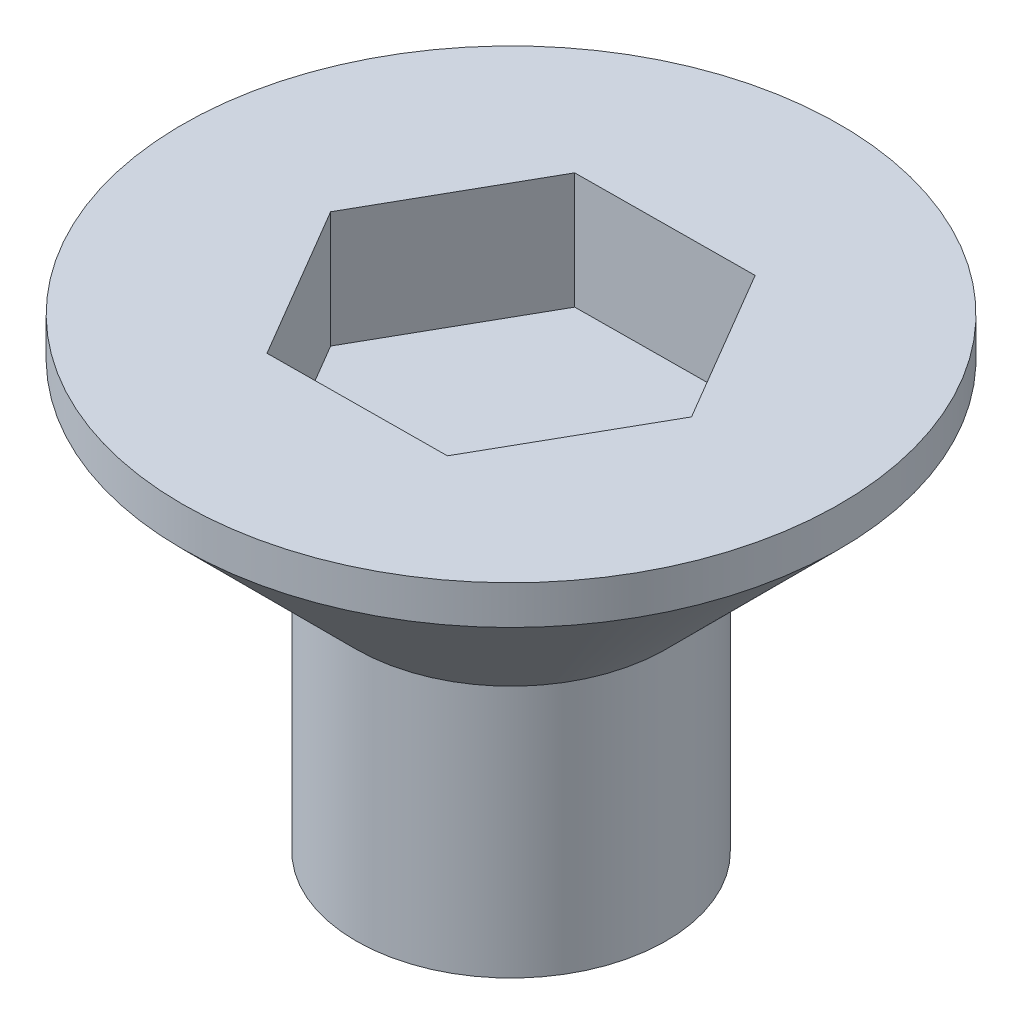
SolidWorks part; units mm, degrees
ref_plane "Спереди" through (0, 0, 0) normal (0, 0, 1) x (1, 0, 0)
ref_plane "Сверху" through (0, 0, 0) normal (0, 1, 0) x (1, 0, 0)
ref_plane "Справа" through (0, 0, 0) normal (1, 0, 0) x (0, 0, -1)
sketch "Эскиз1" plane through (0, 0, 0) normal (0, 0, 1) x (1, 0, 0)
  line L0 (0, 0) -> (4, 0)
  line L1 (4, 0) -> (4, 6.5194)
  line L2 (4, 6.5194) -> (8.4806, 11)
  line L3 (8.4806, 11) -> (8.4806, 12)
  line L4 (8.4806, 12) -> (0, 12)
  line L5 (0, 68.6446) -> (0, -29.1082) construction
  line L6 (0, 0) -> (0, 12)
revolve "Повернуть1" add sketch "Эскиз1" angle 360 about L5
sketch "Эскиз2" plane through (0, 12, 0) normal (0, 1, 0) x (1, 0, 0)
  line L1 (2.3404, -3.982) -> (4.6187, 0.0358)
  line L2 (4.6187, 0.0358) -> (2.2783, 4.0178)
  line L3 (2.2783, 4.0178) -> (-2.3404, 3.982)
  line L4 (-2.3404, 3.982) -> (-4.6187, -0.0358)
  line L5 (-4.6187, -0.0358) -> (-2.2783, -4.0178)
  line L6 (-2.2783, -4.0178) -> (2.3404, -3.982)
  circle A0 centre (0, 0) radius 4 construction
extrude "Вырез-Вытянуть1" cut sketch "Эскиз2" against normal blind 3
